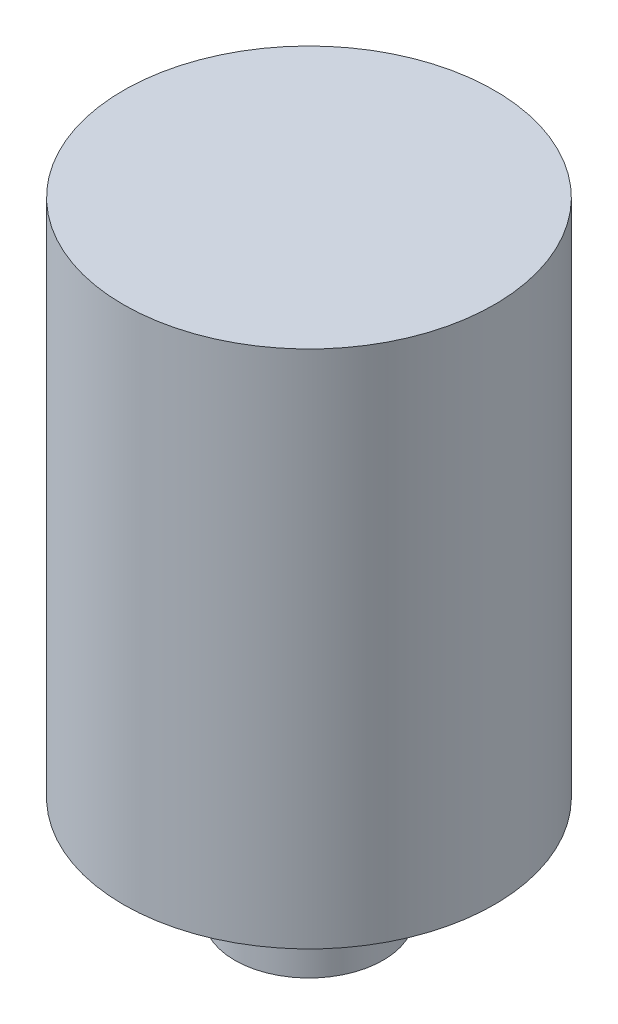
SolidWorks part; units mm, degrees
material "ABS"
ref_plane "Front Plane" through (0, 0, 0) normal (0, 0, 1) x (1, 0, 0)
ref_plane "Top Plane" through (0, 0, 0) normal (0, 1, 0) x (1, 0, 0)
ref_plane "Right Plane" through (0, 0, 0) normal (1, 0, 0) x (0, 0, -1)
sketch "Sketch1" plane through (0, 0, 0) normal (0, 1, 0) x (1, 0, 0)
  circle A0 centre (0, 0) radius 2
  dimension "D1" = 4
extrude "Boss-Extrude1" add sketch "Sketch1" along normal blind 2.8
ref_plane "Plane1" through (0, 2.8, 0) normal (0, 1, 0) x (-1, 0, 0)
sketch "Sketch2" plane through (0, 2.8, 0) normal (0, 1, 0) x (-1, 0, 0)
  circle A0 centre (0, 0) radius 5
  dimension "D1" = 10
extrude "Boss-Extrude2" add sketch "Sketch2" along normal blind 14
